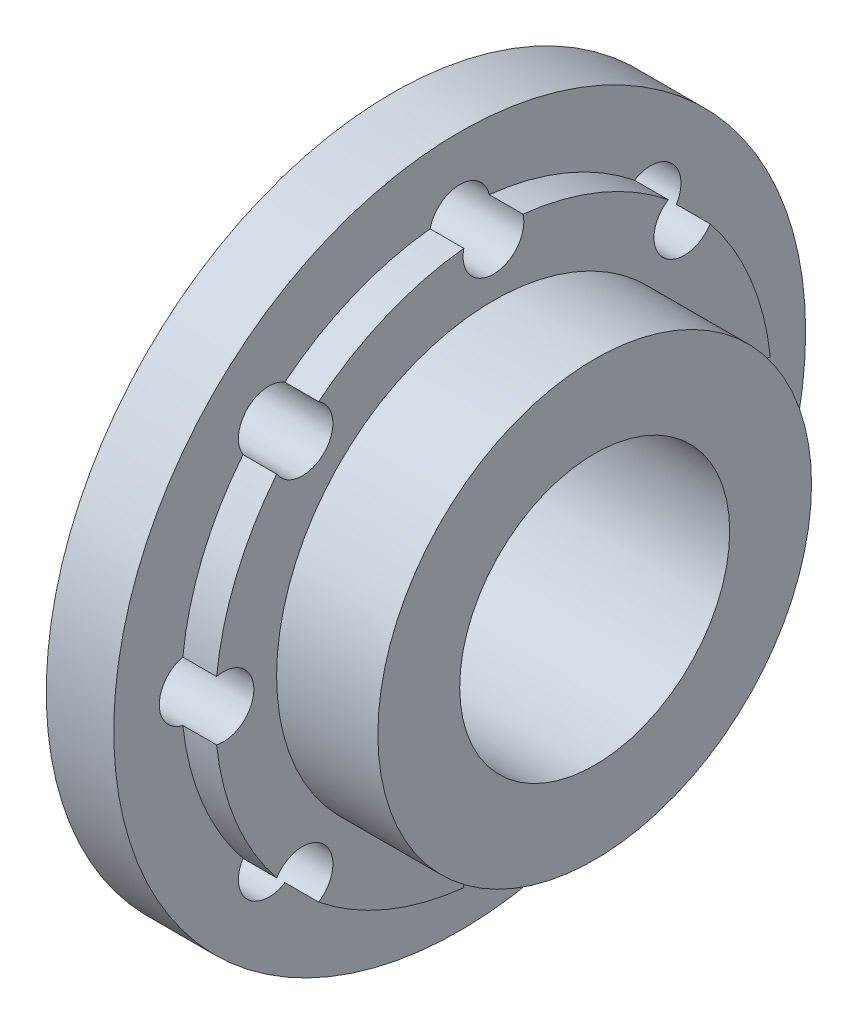
SolidWorks part; units mm, degrees
ref_plane "Front Plane" through (0, 0, 0) normal (0, 0, 1) x (1, 0, 0)
ref_plane "Top Plane" through (0, 0, 0) normal (0, 1, 0) x (1, 0, 0)
ref_plane "Right Plane" through (0, 0, 0) normal (1, 0, 0) x (0, 0, -1)
sketch "Sketch1" plane through (0, 0, 0) normal (0, 0, 1) x (1, 0, 0)
  line L0 (0, 4) -> (0, 6.5)
  line L1 (0, 6.5) -> (-3, 6.5)
  line L2 (-3, 6.5) -> (-3, 8.5)
  line L3 (-3, 8.5) -> (-4, 8.5)
  line L4 (-4, 8.5) -> (-4, 10.25)
  line L5 (-4, 10.25) -> (-6, 10.25)
  line L6 (-6, 10.25) -> (-6, 4)
  line L7 (-6, 4) -> (0, 4)
  line L8 (0, 0) -> (-6, 0) construction
  dimension "D1" = 6.5
  dimension "D2" = 4
  dimension "D3" = 8.5
  dimension "D4" = 10.25
  dimension "D5" = 1
  dimension "D6" = 2
  dimension "D7" = 4
revolve "Revolve1" add sketch "Sketch1" angle 360 about L8
other "Move Face1" face at (-3, 0, -6.5) parameters "D1"=0.075
other "Move Face2" face at (-4, 0, -8.5) parameters "D1"=0.25
sketch "Sketch2" plane through (-6, 0, 0) normal (-1, 0, 0) x (0, 0, 1)
  line L0 (0, 0) -> (0, 8) construction
  circle A0 centre (0, 8) radius 0.9
  circle A1 centre (5.6569, 5.6569) radius 0.9
  circle A2 centre (8, 0) radius 0.9
  circle A3 centre (5.6569, -5.6569) radius 0.9
  circle A4 centre (0, -8) radius 0.9
  circle A5 centre (-5.6569, -5.6569) radius 0.9
  circle A6 centre (-8, 0) radius 0.9
  circle A7 centre (-5.6569, 5.6569) radius 0.9
  point P4 (12.1626, -0.4416)
  point P5 (0, 0)
  point P21 (0, 0)
  dimension "D1" = 1.8
  dimension "D2" = 8
  dimension "D3" = 8
extrude "Cut-Extrude1" cut sketch "Sketch2" against normal through all
